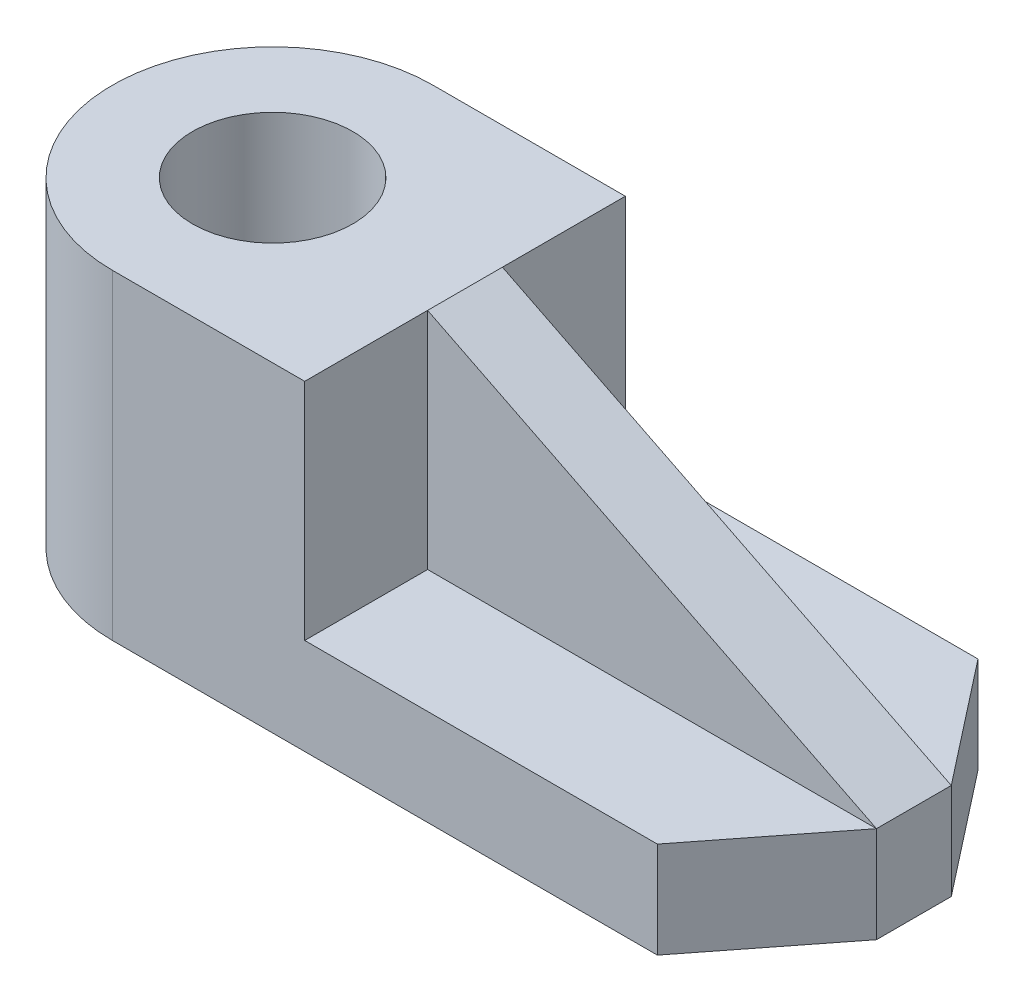
SolidWorks part; units mm, degrees
ref_plane "Alzado" through (0, 0, 0) normal (0, 0, 1) x (1, 0, 0)
ref_plane "Planta" through (0, 0, 0) normal (0, 1, 0) x (1, 0, 0)
ref_plane "Vista lateral" through (0, 0, 0) normal (1, 0, 0) x (0, 0, -1)
sketch "Croquis5" plane through (0, 0, 0) normal (0, 1, 0) x (1, 0, 0)
  line L0 (0, 15) -> (18, 15)
  line L1 (18, 15) -> (18, -15)
  line L2 (18, -15) -> (0, -15)
  line L8 (0, 0) -> (18, 0) construction
  arc A0 (0, 15) -> (0, -15) centre (0, 0) ccw
  circle A1 centre (0, 0) radius 7.5
  point P12 (60, 0)
  dimension "D1" = 30
  dimension "D3" = 15
  dimension "D2" = 18
sketch "Croquis6" plane through (0, 0, 0) normal (0, 1, 0) x (1, 0, 0)
  line L1 (18, 15) -> (18, -15)
  line L3 (18, 15) -> (51, 15)
  line L4 (51, 15) -> (60, 3.5)
  line L5 (60, 3.5) -> (60, -3.5)
  line L6 (60, -3.5) -> (51, -15)
  line L7 (51, -15) -> (18, -15)
  line L9 (18, 0) -> (60, 0) construction
  point P12 (60, 0)
  dimension "D5" = 9
  dimension "D6" = 9
  dimension "D7" = 7
extrude "Saliente-Extruir3" add sketch "Croquis5" along normal blind 30
extrude "Saliente-Extruir4" add sketch "Croquis6" along normal blind 9
sketch "Croquis8" plane through (0, 0, 0) normal (0, 0, 1) x (1, 0, 0)
  line L0 (18, 30) -> (60, 9)
  line L1 (60, 9) -> (18, 9)
  line L2 (18, 9) -> (18, 30)
extrude "Saliente-Extruir5" add sketch "Croquis8" along normal blind 3.5 and the other way blind 3.5
